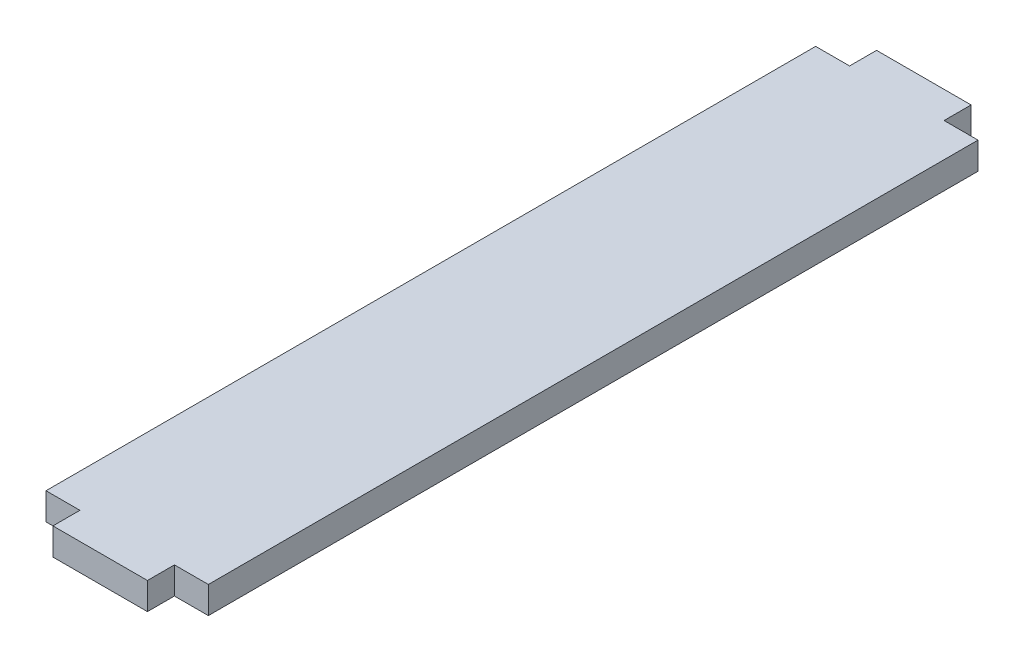
SolidWorks part; units mm, degrees
ref_plane "Front Plane" through (0, 0, 0) normal (0, 0, 1) x (1, 0, 0)
ref_plane "Top Plane" through (0, 0, 0) normal (0, 1, 0) x (1, 0, 0)
ref_plane "Right Plane" through (0, 0, 0) normal (1, 0, 0) x (0, 0, -1)
sketch "Sketch1" plane through (0, 0, 0) normal (0, 1, 0) x (1, 0, 0)
  line L1 (0, 0) -> (-30.54, 0)
  line L2 (0, 0) -> (0, 144.78)
  line L3 (0, 144.78) -> (-30.54, 144.78)
  line L4 (-30.54, 0) -> (-30.54, 144.78)
  dimension "D1" = 144.78
  dimension "D2" = 30.54
extrude "Boss-Extrude1" add sketch "Sketch1" along normal blind 5.08
sketch "Sketch2" plane through (0, 0, 0) normal (0, 0, 1) x (1, 0, 0)
  line L0 (0, 0) -> (-6.38, 0) construction
  line L1 (-30.54, 0) -> (0, 0) construction
  line L2 (-6.38, 0) -> (-24.16, 0) construction
  line L3 (-24.16, 0) -> (-30.54, 0) construction
  line L4 (-30.54, 5.08) -> (0, 5.08) construction
  line L5 (-24.16, 0) -> (-6.38, 0)
  line L6 (-24.16, 0) -> (-24.16, 5.08)
  line L7 (-24.16, 5.08) -> (-6.38, 5.08)
  line L8 (-6.38, 0) -> (-6.38, 5.08)
  dimension "D1" = 17.78
extrude "Boss-Extrude2" add sketch "Sketch2" along normal blind 5.08
sketch "Sketch3" plane through (0, 0, -144.78) normal (0, 0, -1) x (-1, 0, 0)
  line L0 (30.54, 0) -> (24.16, 0) construction
  line L1 (0, 0) -> (30.54, 0) construction
  line L2 (24.16, 0) -> (6.38, 0) construction
  line L3 (6.38, 0) -> (0, 0) construction
  line L4 (0, 5.08) -> (30.54, 5.08) construction
  line L5 (24.16, 0) -> (6.38, 0)
  line L6 (24.16, 0) -> (24.16, 5.08)
  line L7 (24.16, 5.08) -> (6.38, 5.08)
  line L8 (6.38, 0) -> (6.38, 5.08)
  dimension "D1" = 17.78
extrude "Boss-Extrude3" add sketch "Sketch3" along normal blind 5.08
equation "\"MDFThickness\"= .2in"
equation "\"D1@Boss-Extrude1\"=\"MDFThickness\""
equation "\"D1@Boss-Extrude2\"=\"MDFThickness\""
equation "\"D1@Boss-Extrude3\"=\"MDFThickness\""
